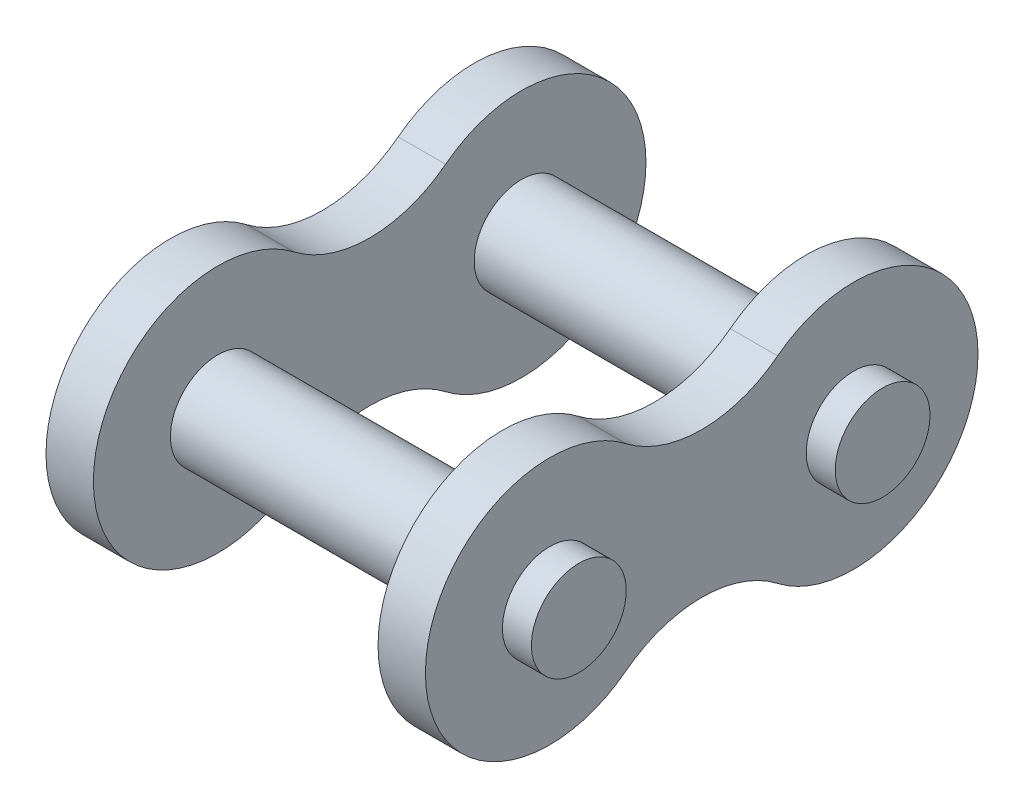
SolidWorks part; units mm, degrees
material "Alloy Steel"
ref_plane "Front" through (0, 0, 0) normal (0, 0, 1) x (1, 0, 0)
ref_plane "Top" through (0, 0, 0) normal (0, 1, 0) x (1, 0, 0)
ref_plane "Right" through (0, 0, 0) normal (1, 0, 0) x (0, 0, -1)
ref_plane "Back Link Plane" through (-11.8999, 0, 0) normal (1, 0, 0) x (0, 0, -1)
ref_plane "Front Link Plane" through (11.8999, 0, 0) normal (1, 0, 0) x (0, 0, -1)
ref_plane "F/F Pin Plane" through (0, 0, 12.7) normal (0, 0, 1) x (1, 0, 0)
ref_plane "F/B Pin Plane" through (0, 0, -12.7) normal (0, 0, 1) x (1, 0, 0)
sketch "Back Link Sketch" plane through (-11.8999, 0, 0) normal (1, 0, 0) x (0, 0, -1)
  line L0 (0, -33.7816) -> (0, 28.0067) construction
  line L1 (59.1569, 0) -> (-51.6942, 0) construction
  arc A0 (-6.35, 8.238) -> (-6.35, -8.238) centre (-12.7, 0) ccw
  arc A1 (-6.35, -8.238) -> (6.35, -8.238) centre (0, -16.476) cw
  arc A2 (6.35, -8.238) -> (6.35, 8.238) centre (12.7, 0) ccw
  arc A3 (6.35, 8.238) -> (-6.35, 8.238) centre (0, 16.476) cw
  circle A4 centre (-12.7, 0) radius 3.9624
  circle A5 centre (12.7, 0) radius 3.9624
  dimension "D" = 7.9248
  dimension "Ho" = 20.8026
  dimension "Ho-1" = 10.4013
  dimension "P" = 25.4
  dimension "P-1" = 12.7
  dimension "Ho-2" = 20.8026
  dimension "Ho-3" = 20.8026
extrude "Back Link Extrude" add sketch "Back Link Sketch" against normal blind 3.9624
sketch "Front Link Sketch" plane through (11.8999, 0, 0) normal (1, 0, 0) x (0, 0, -1)
  circle A0 centre (-12.7, 0) radius 3.9624 construction
  circle A1 centre (12.7, 0) radius 3.9624 construction
  circle A2 centre (-12.7, 0) radius 3.9624
  circle A3 centre (12.7, 0) radius 3.9624
  arc A4 (-6.35, 8.238) -> (6.35, 8.238) centre (0, 16.476) ccw
  arc A5 (-6.35, 8.238) -> (-6.35, -8.238) centre (-12.7, 0) ccw
  arc A6 (6.35, -8.238) -> (-6.35, -8.238) centre (0, -16.476) ccw
  arc A7 (6.35, -8.238) -> (6.35, 8.238) centre (12.7, 0) ccw
  arc A8 (-6.35, 8.238) -> (6.35, 8.238) centre (0, 16.476) ccw
  arc A9 (-6.35, 8.238) -> (-6.35, -8.238) centre (-12.7, 0) ccw
  arc A10 (6.35, -8.238) -> (-6.35, -8.238) centre (0, -16.476) ccw
  arc A11 (6.35, -8.238) -> (6.35, 8.238) centre (12.7, 0) ccw
  dimension "D1" = 0
extrude "Front Link Extrude" add sketch "Front Link Sketch" along normal blind 3.9624
sketch "Pin Sketch" plane through (0, 0, 0) normal (1, 0, 0) x (0, 0, -1)
  circle A0 centre (12.7, 0) radius 3.9624 construction
  circle A1 centre (-12.7, 0) radius 3.9624 construction
  circle A2 centre (12.7, 0) radius 3.9624
  circle A3 centre (-12.7, 0) radius 3.9624
extrude "Pin Extrude" add sketch "Pin Sketch" along normal blind 18.288 and the other way blind 18.288
ref_point "Pin Point 1"
ref_point "Pin Point 2"
equation "\"D1@F/F Pin Plane\" = \"P@Back Link Sketch\" * 0.50"
equation "\"D1@F/B Pin Plane\" = \"P@Back Link Sketch\" * 0.50"
equation "\"Ho-1@Back Link Sketch\" = \"Ho@Back Link Sketch\" * 0.50"
equation "\"Ho-2@Back Link Sketch\" = \"Ho@Back Link Sketch\""
equation "\"Ho-3@Back Link Sketch\" = \"Ho@Back Link Sketch\""
equation "\"P-1@Back Link Sketch\" = \"P@Back Link Sketch\" * 0.50"
equation "\"D1@Front Link Plane\" = \"D1@Back Link Plane\""
equation "\"D1@Front Link Extrude\" = \"D1@Back Link Extrude\""
equation "\"D2@Pin Extrude\" = \"D1@Pin Extrude\""
